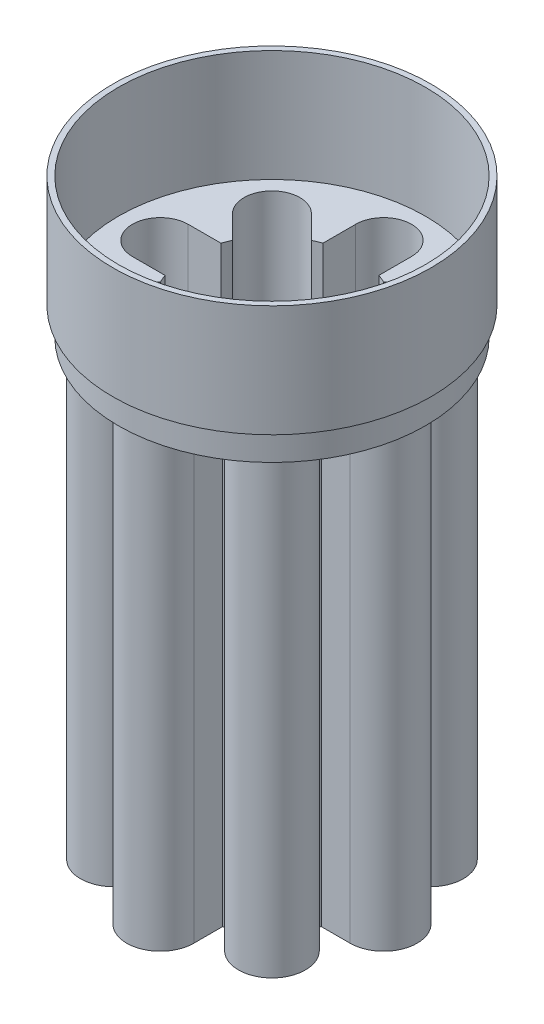
SolidWorks part; units mm, degrees
ref_plane "Front Plane" through (0, 0, 0) normal (0, 0, 1) x (1, 0, 0)
ref_plane "Top Plane" through (0, 0, 0) normal (0, 1, 0) x (1, 0, 0)
ref_plane "Right Plane" through (0, 0, 0) normal (1, 0, 0) x (0, 0, -1)
sketch "Sketch1" plane through (0, 0, 0) normal (0, 1, 0) x (1, 0, 0)
  line L0 (5, 20) -> (5, 14.1421)
  line L1 (-5, 20) -> (-5, 14.1421)
  line L2 (10.6066, 17.6777) -> (6.4645, 13.5355)
  line L3 (17.6777, 10.6066) -> (13.5355, 6.4645)
  line L4 (20, 5) -> (14.1421, 5)
  line L5 (20, -5) -> (14.1421, -5)
  line L6 (17.6777, -10.6066) -> (13.5355, -6.4645)
  line L7 (10.6066, -17.6777) -> (6.4645, -13.5355)
  line L8 (5, -20) -> (5, -14.1421)
  line L9 (-5, -20) -> (-5, -14.1421)
  line L10 (-10.6066, -17.6777) -> (-6.4645, -13.5355)
  line L11 (-17.6777, -10.6066) -> (-13.5355, -6.4645)
  line L12 (-20, -5) -> (-14.1421, -5)
  line L13 (-20, 5) -> (-14.1421, 5)
  line L14 (-17.6777, 10.6066) -> (-13.5355, 6.4645)
  line L15 (-10.6066, 17.6777) -> (-6.4645, 13.5355)
  arc A1 (-14.1421, -5) -> (-13.5355, -6.4645) centre (0, 0) ccw
  arc A4 (5, 20) -> (-5, 20) centre (0, 20) ccw
  arc A5 (17.6777, 10.6066) -> (10.6066, 17.6777) centre (14.1421, 14.1421) ccw
  arc A6 (20, -5) -> (20, 5) centre (20, 0) ccw
  arc A7 (10.6066, -17.6777) -> (17.6777, -10.6066) centre (14.1421, -14.1421) ccw
  arc A8 (-5, -20) -> (5, -20) centre (0, -20) ccw
  arc A9 (-17.6777, -10.6066) -> (-10.6066, -17.6777) centre (-14.1421, -14.1421) ccw
  arc A10 (-20, 5) -> (-20, -5) centre (-20, 0) ccw
  arc A11 (-10.6066, 17.6777) -> (-17.6777, 10.6066) centre (-14.1421, 14.1421) ccw
  arc A12 (-13.5355, 6.4645) -> (-14.1421, 5) centre (0, 0) ccw
  arc A13 (-5, 14.1421) -> (-6.4645, 13.5355) centre (0, 0) ccw
  arc A14 (6.4645, 13.5355) -> (5, 14.1421) centre (0, 0) ccw
  arc A15 (14.1421, 5) -> (13.5355, 6.4645) centre (0, 0) ccw
  arc A16 (13.5355, -6.4645) -> (14.1421, -5) centre (0, 0) ccw
  arc A17 (5, -14.1421) -> (6.4645, -13.5355) centre (0, 0) ccw
  arc A18 (-6.4645, -13.5355) -> (-5, -14.1421) centre (0, 0) ccw
  point P47 (0, 0)
  dimension "D2" = 30
  dimension "D3" = 8
  dimension "D5" = 5
extrude "Extrude-Thin1" add sketch "Sketch1" along normal blind 80 thin thin type one direction wall 1
sketch "Sketch2" plane through (0, 0, 0) normal (0, -1, 0) x (1, 0, 0)
  line L184 (14.7307, 6.2454) -> (18.3848, 9.8995)
  line L185 (9.8995, 18.3848) -> (6.2454, 14.7307)
  line L186 (6, 14.8324) -> (6, 20)
  line L187 (-6, 20) -> (-6, 14.8324)
  line L188 (-6.2454, 14.7307) -> (-9.8995, 18.3848)
  line L189 (-18.3848, 9.8995) -> (-14.7307, 6.2454)
  line L190 (20, 6) -> (14.8324, 6)
  line L191 (14.8324, -6) -> (20, -6)
  line L192 (18.3848, -9.8995) -> (14.7307, -6.2454)
  line L193 (6.2454, -14.7307) -> (9.8995, -18.3848)
  line L194 (6, -20) -> (6, -14.8324)
  line L195 (-6, -14.8324) -> (-6, -20)
  line L196 (-9.8995, -18.3848) -> (-6.2454, -14.7307)
  line L197 (-14.7307, -6.2454) -> (-18.3848, -9.8995)
  line L198 (-20, -6) -> (-14.8324, -6)
  line L199 (-14.8324, 6) -> (-20, 6)
  line L200 (14.7307, 6.2454) -> (18.3848, 9.8995)
  line L201 (9.8995, 18.3848) -> (6.2454, 14.7307)
  line L202 (6, 14.8324) -> (6, 20)
  line L203 (-6, 20) -> (-6, 14.8324)
  line L204 (-6.2454, 14.7307) -> (-9.8995, 18.3848)
  line L205 (-18.3848, 9.8995) -> (-14.7307, 6.2454)
  line L206 (20, 6) -> (14.8324, 6)
  line L207 (14.8324, -6) -> (20, -6)
  line L208 (18.3848, -9.8995) -> (14.7307, -6.2454)
  line L209 (6.2454, -14.7307) -> (9.8995, -18.3848)
  line L210 (6, -20) -> (6, -14.8324)
  line L211 (-6, -14.8324) -> (-6, -20)
  line L212 (-9.8995, -18.3848) -> (-6.2454, -14.7307)
  line L213 (-14.7307, -6.2454) -> (-18.3848, -9.8995)
  line L214 (-20, -6) -> (-14.8324, -6)
  line L215 (-14.8324, 6) -> (-20, 6)
  arc A190 (18.3848, 9.8995) -> (9.8995, 18.3848) centre (14.1421, 14.1421) ccw
  arc A191 (6.2454, 14.7307) -> (6, 14.8324) centre (0, 0) ccw
  arc A192 (6, 20) -> (-6, 20) centre (0, 20) ccw
  arc A193 (-6, 14.8324) -> (-6.2454, 14.7307) centre (0, 0) ccw
  arc A194 (-9.8995, 18.3848) -> (-18.3848, 9.8995) centre (-14.1421, 14.1421) ccw
  arc A195 (14.8324, 6) -> (14.7307, 6.2454) centre (0, 0) ccw
  arc A196 (20, -6) -> (20, 6) centre (20, 0) ccw
  arc A197 (14.7307, -6.2454) -> (14.8324, -6) centre (0, 0) ccw
  arc A198 (9.8995, -18.3848) -> (18.3848, -9.8995) centre (14.1421, -14.1421) ccw
  arc A199 (6, -14.8324) -> (6.2454, -14.7307) centre (0, 0) ccw
  arc A200 (-6, -20) -> (6, -20) centre (0, -20) ccw
  arc A201 (-6.2454, -14.7307) -> (-6, -14.8324) centre (0, 0) ccw
  arc A202 (-18.3848, -9.8995) -> (-9.8995, -18.3848) centre (-14.1421, -14.1421) ccw
  arc A203 (-14.8324, -6) -> (-14.7307, -6.2454) centre (0, 0) ccw
  arc A204 (-20, 6) -> (-20, -6) centre (-20, 0) ccw
  arc A205 (-14.7307, 6.2454) -> (-14.8324, 6) centre (0, 0) ccw
  arc A206 (18.3848, 9.8995) -> (9.8995, 18.3848) centre (14.1421, 14.1421) ccw
  arc A207 (6.2454, 14.7307) -> (6, 14.8324) centre (0, 0) ccw
  arc A208 (6, 20) -> (-6, 20) centre (0, 20) ccw
  arc A209 (-6, 14.8324) -> (-6.2454, 14.7307) centre (0, 0) ccw
  arc A210 (-9.8995, 18.3848) -> (-18.3848, 9.8995) centre (-14.1421, 14.1421) ccw
  arc A211 (14.8324, 6) -> (14.7307, 6.2454) centre (0, 0) ccw
  arc A212 (20, -6) -> (20, 6) centre (20, 0) ccw
  arc A213 (14.7307, -6.2454) -> (14.8324, -6) centre (0, 0) ccw
  arc A214 (9.8995, -18.3848) -> (18.3848, -9.8995) centre (14.1421, -14.1421) ccw
  arc A215 (6, -14.8324) -> (6.2454, -14.7307) centre (0, 0) ccw
  arc A216 (-6, -20) -> (6, -20) centre (0, -20) ccw
  arc A217 (-6.2454, -14.7307) -> (-6, -14.8324) centre (0, 0) ccw
  arc A218 (-18.3848, -9.8995) -> (-9.8995, -18.3848) centre (-14.1421, -14.1421) ccw
  arc A219 (-14.8324, -6) -> (-14.7307, -6.2454) centre (0, 0) ccw
  arc A220 (-20, 6) -> (-20, -6) centre (-20, 0) ccw
  arc A221 (-14.7307, 6.2454) -> (-14.8324, 6) centre (0, 0) ccw
  dimension "D1" = 1
extrude "Boss-Extrude1" add sketch "Sketch2" along normal blind 1
sketch "Sketch3" plane through (0, 80, 0) normal (0, 1, 0) x (1, 0, 0)
  line L291 (-20, -5) -> (-14.1421, -5)
  line L292 (-13.5355, -6.4645) -> (-17.6777, -10.6066)
  line L293 (-10.6066, -17.6777) -> (-6.4645, -13.5355)
  line L294 (-5, -14.1421) -> (-5, -20)
  line L295 (5, -20) -> (5, -14.1421)
  line L296 (6.4645, -13.5355) -> (10.6066, -17.6777)
  line L297 (17.6777, -10.6066) -> (13.5355, -6.4645)
  line L298 (14.1421, -5) -> (20, -5)
  line L299 (20, 5) -> (14.1421, 5)
  line L300 (13.5355, 6.4645) -> (17.6777, 10.6066)
  line L301 (10.6066, 17.6777) -> (6.4645, 13.5355)
  line L302 (5, 14.1421) -> (5, 20)
  line L303 (-5, 20) -> (-5, 14.1421)
  line L304 (-6.4645, 13.5355) -> (-10.6066, 17.6777)
  line L305 (-17.6777, 10.6066) -> (-13.5355, 6.4645)
  line L306 (-14.1421, 5) -> (-20, 5)
  line L307 (-20, -5) -> (-14.1421, -5)
  line L308 (-13.5355, -6.4645) -> (-17.6777, -10.6066)
  line L309 (-10.6066, -17.6777) -> (-6.4645, -13.5355)
  line L310 (-5, -14.1421) -> (-5, -20)
  line L311 (5, -20) -> (5, -14.1421)
  line L312 (6.4645, -13.5355) -> (10.6066, -17.6777)
  line L313 (17.6777, -10.6066) -> (13.5355, -6.4645)
  line L314 (14.1421, -5) -> (20, -5)
  line L315 (20, 5) -> (14.1421, 5)
  line L316 (13.5355, 6.4645) -> (17.6777, 10.6066)
  line L317 (10.6066, 17.6777) -> (6.4645, 13.5355)
  line L318 (5, 14.1421) -> (5, 20)
  line L319 (-5, 20) -> (-5, 14.1421)
  line L320 (-6.4645, 13.5355) -> (-10.6066, 17.6777)
  line L321 (-17.6777, 10.6066) -> (-13.5355, 6.4645)
  line L322 (-14.1421, 5) -> (-20, 5)
  circle A0 centre (0, 0) radius 27.5
  arc A308 (-14.1421, -5) -> (-13.5355, -6.4645) centre (0, 0) ccw
  arc A309 (-17.6777, -10.6066) -> (-10.6066, -17.6777) centre (-14.1421, -14.1421) ccw
  arc A310 (-6.4645, -13.5355) -> (-5, -14.1421) centre (0, 0) ccw
  arc A311 (-5, -20) -> (5, -20) centre (0, -20) ccw
  arc A312 (5, -14.1421) -> (6.4645, -13.5355) centre (0, 0) ccw
  arc A313 (10.6066, -17.6777) -> (17.6777, -10.6066) centre (14.1421, -14.1421) ccw
  arc A314 (13.5355, -6.4645) -> (14.1421, -5) centre (0, 0) ccw
  arc A315 (20, -5) -> (20, 5) centre (20, 0) ccw
  arc A316 (14.1421, 5) -> (13.5355, 6.4645) centre (0, 0) ccw
  arc A317 (17.6777, 10.6066) -> (10.6066, 17.6777) centre (14.1421, 14.1421) ccw
  arc A318 (6.4645, 13.5355) -> (5, 14.1421) centre (0, 0) ccw
  arc A319 (5, 20) -> (-5, 20) centre (0, 20) ccw
  arc A320 (-5, 14.1421) -> (-6.4645, 13.5355) centre (0, 0) ccw
  arc A321 (-10.6066, 17.6777) -> (-17.6777, 10.6066) centre (-14.1421, 14.1421) ccw
  arc A322 (-13.5355, 6.4645) -> (-14.1421, 5) centre (0, 0) ccw
  arc A323 (-20, 5) -> (-20, -5) centre (-20, 0) ccw
  arc A324 (-14.1421, -5) -> (-13.5355, -6.4645) centre (0, 0) ccw
  arc A325 (-17.6777, -10.6066) -> (-10.6066, -17.6777) centre (-14.1421, -14.1421) ccw
  arc A326 (-6.4645, -13.5355) -> (-5, -14.1421) centre (0, 0) ccw
  arc A327 (-5, -20) -> (5, -20) centre (0, -20) ccw
  arc A328 (5, -14.1421) -> (6.4645, -13.5355) centre (0, 0) ccw
  arc A329 (10.6066, -17.6777) -> (17.6777, -10.6066) centre (14.1421, -14.1421) ccw
  arc A330 (13.5355, -6.4645) -> (14.1421, -5) centre (0, 0) ccw
  arc A331 (20, -5) -> (20, 5) centre (20, 0) ccw
  arc A332 (14.1421, 5) -> (13.5355, 6.4645) centre (0, 0) ccw
  arc A333 (17.6777, 10.6066) -> (10.6066, 17.6777) centre (14.1421, 14.1421) ccw
  arc A334 (6.4645, 13.5355) -> (5, 14.1421) centre (0, 0) ccw
  arc A335 (5, 20) -> (-5, 20) centre (0, 20) ccw
  arc A336 (-5, 14.1421) -> (-6.4645, 13.5355) centre (0, 0) ccw
  arc A337 (-10.6066, 17.6777) -> (-17.6777, 10.6066) centre (-14.1421, 14.1421) ccw
  arc A338 (-13.5355, 6.4645) -> (-14.1421, 5) centre (0, 0) ccw
  arc A339 (-20, 5) -> (-20, -5) centre (-20, 0) ccw
  dimension "D1" = 55
  dimension "D2" = 1
extrude "Boss-Extrude2" add sketch "Sketch3" along normal blind 5
sketch "Sketch4" plane through (0, 85, 0) normal (0, 1, 0) x (1, 0, 0)
  circle A0 centre (0, 0) radius 27.5
  dimension "D1" = 55
extrude "Extrude-Thin2" add sketch "Sketch4" along normal blind 20 separate body thin
